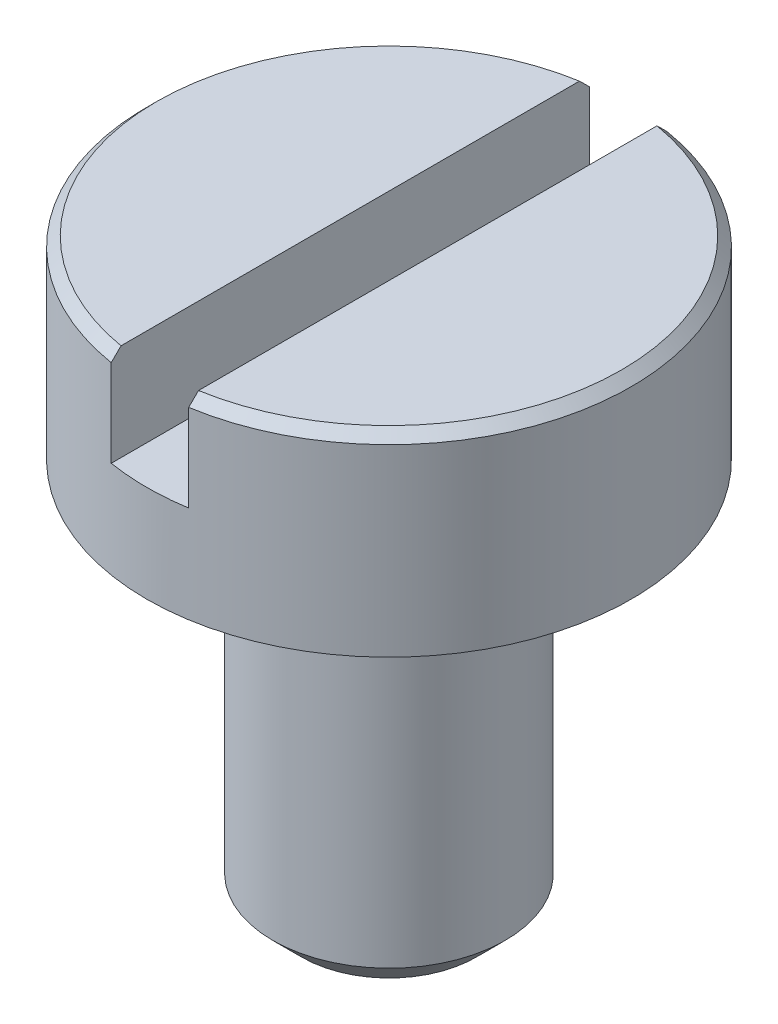
SolidWorks part; units mm, degrees
ref_plane "Alzado" through (0, 0, 0) normal (0, 0, 1) x (1, 0, 0)
ref_plane "Planta" through (0, 0, 0) normal (0, 1, 0) x (1, 0, 0)
ref_plane "Vista lateral" through (0, 0, 0) normal (1, 0, 0) x (0, 0, -1)
sketch "Sketch1" plane through (0, 0, 0) normal (0, 1, 0) x (1, 0, 0)
  circle A0 centre (0, 0) radius 1.25
  dimension "D1" = 2.5
extrude "Boss-Extrude1" add sketch "Sketch1" along normal blind 1
sketch "Sketch2" plane through (0, 0, 0) normal (0, 1, 0) x (1, 0, 0)
  circle A0 centre (0, 0) radius 0.6
  dimension "D1" = 1.2
extrude "Boss-Extrude2" add sketch "Sketch2" against normal blind 2
chamfer "Chamfer1" distance 0.05 angle 45 1 edges at (0, 1, 1.25)
chamfer "Chamfer2" distance 0.15 angle 45 1 edges at (0, -2, 0.6)
sketch "Sketch3" plane through (0, 0, 0) normal (0, 0, 1) x (1, 0, 0)
  line L0 (0, -1000) -> (0, 49000) construction
  line L1 (1.2, 1) -> (-1.2, 1) construction
  line L2 (-0.2, -999.9073) -> (-0.2, 49000.0927) construction
  line L3 (1.2, 1) -> (-1.2, 1) construction
  line L4 (-1000.8273, 0.5) -> (48999.1727, 0.5) construction
  line L5 (-0.2, 1) -> (0, 1)
  line L6 (-0.2, 1) -> (-0.2, 0.5)
  line L7 (0.2, 0.5) -> (0, 0.5)
  line L8 (-0.2, 0.5) -> (0, 0.5)
  line L9 (0.2, 1) -> (0.2, 0.5)
  line L10 (0.2, 1) -> (0, 1)
  dimension "D1" = 0.5
  dimension "D2" = 0.2
extrude "Cut-Extrude1" cut sketch "Sketch3" against normal through all both and the other way through all
